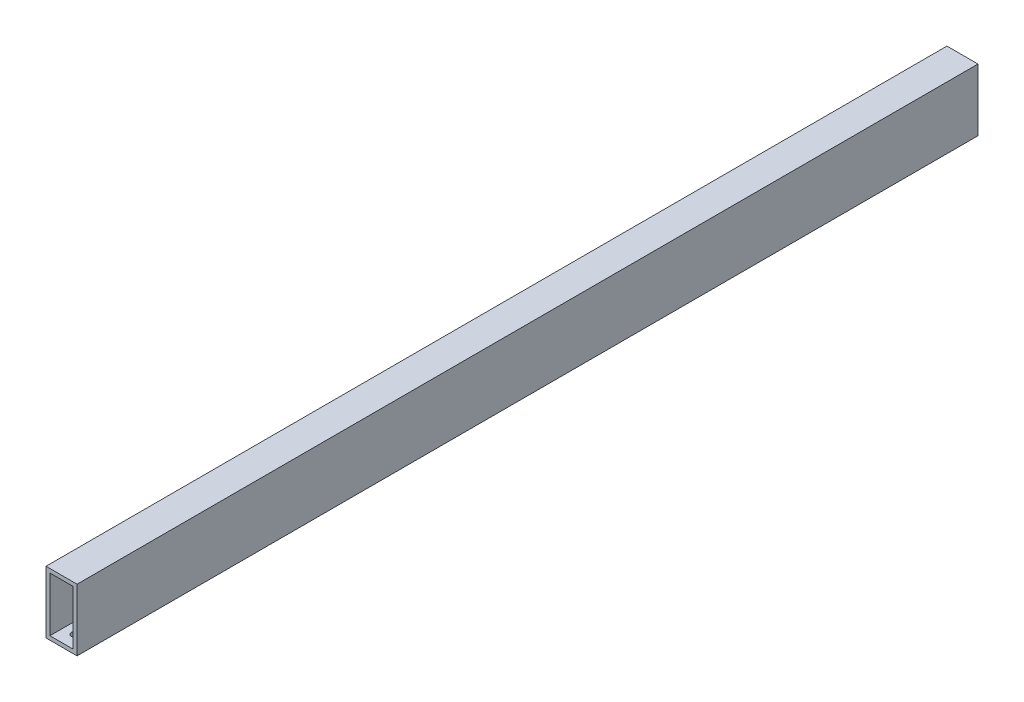
SolidWorks part; units mm, degrees
material "6061-T6 (SS)"
ref_plane "Front Plane" through (0, 0, 0) normal (0, 0, 1) x (1, 0, 0)
ref_plane "Top Plane" through (0, 0, 0) normal (0, 1, 0) x (1, 0, 0)
ref_plane "Right Plane" through (0, 0, 0) normal (1, 0, 0) x (0, 0, -1)
sketch "Sketch1" plane through (0, 0, 0) normal (0, 0, 1) x (1, 0, 0)
  line L0 (3.175, 3.175) -> (3.175, 47.625)
  line L1 (0, 0) -> (25.4, 0)
  line L2 (0, 0) -> (0, 50.8)
  line L3 (0, 50.8) -> (25.4, 50.8)
  line L4 (25.4, 0) -> (25.4, 50.8)
  line L5 (3.175, 47.625) -> (22.225, 47.625)
  line L6 (22.225, 3.175) -> (22.225, 47.625)
  line L7 (3.175, 3.175) -> (22.225, 3.175)
  dimension "D1" = 25.4
  dimension "D2" = 50.8
  dimension "D3" = 3.175
extrude "Boss-Extrude1" add sketch "Sketch1" along normal blind 736.6
sketch "Sketch4" plane through (0, 0, 0) normal (0, -1, 0) x (1, 0, 0)
  line L0 (0, 368.3) -> (25.4, 368.3)
  line L1 (0, 736.6) -> (0, 0) construction
  line L2 (25.4, 736.6) -> (25.4, 0) construction
  circle A5 centre (12.7, 11.43) radius 3.175
  circle A6 centre (12.7, 11.43) radius 3.175
  circle A7 centre (12.7, 26.0582) radius 3.175
  circle A8 centre (12.7, 26.0582) radius 3.175
  circle A30 centre (12.7, 710.5418) radius 3.175
  circle A31 centre (12.7, 725.17) radius 3.175
  dimension "D3" = 0
  dimension "D4" = 0
extrude "Cut-Extrude1" cut sketch "Sketch4" against normal up to surface (3.175 mm away) contours A30 | A31 | A6 | A8 up to face at (12.7, 3.175, 368.3)
